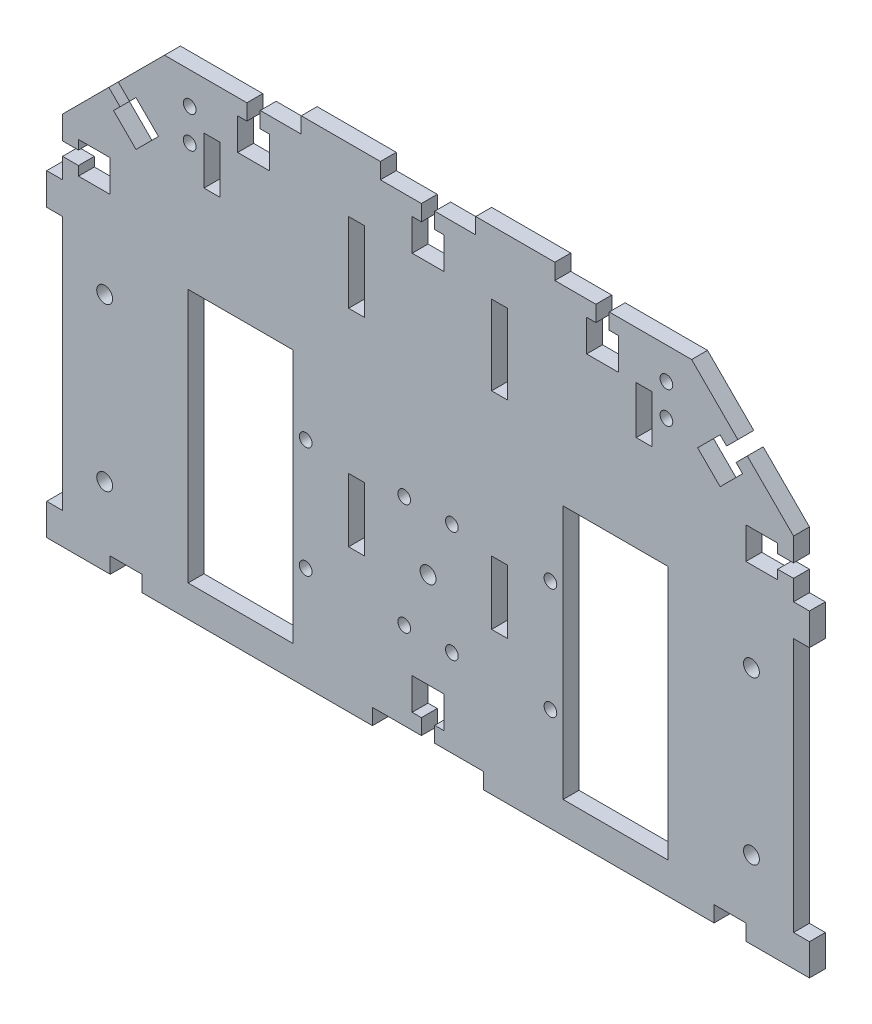
SolidWorks part; units mm, degrees
ref_plane "Front Plane" through (0, 0, 0) normal (0, 0, 1) x (1, 0, 0)
ref_plane "Top Plane" through (0, 0, 0) normal (0, 1, 0) x (1, 0, 0)
ref_plane "Right Plane" through (0, 0, 0) normal (1, 0, 0) x (0, 0, -1)
sketch "Sketch1" plane through (0, 0, 0) normal (0, 0, 1) x (1, 0, 0)
  line L28 (-42.5, -77.4) -> (-23.1006, -77.4) construction
  line L29 (42.5, -104.9) -> (-42.5, -104.9)
  line L30 (42.5, -104.9) -> (42.5, -49.9)
  line L32 (-42.5, -104.9) -> (-42.5, -49.9)
  line L57 (-42.5, -49.9) -> (-42.5, -37.4)
  line L58 (42.5, -49.9) -> (42.5, -37.4)
  line L89 (-120, -17.4) -> (-120, -37.4)
  line L91 (120, -37.4) -> (120, -17.4)
  line L101 (120, -17.4) -> (115, -17.4)
  line L102 (115, -17.4) -> (115, 12.8)
  line L103 (115, 12.8) -> (120, 12.8)
  line L104 (120, 12.8) -> (120, 27.7)
  line L105 (120, 27.7) -> (100.1, 27.7)
  line L106 (100.1, 27.7) -> (100.1, 22.7)
  line L107 (100.1, 22.7) -> (39.9, 22.7)
  line L108 (39.9, 22.7) -> (39.9, 27.7)
  line L109 (39.9, 27.7) -> (-39.9, 27.7)
  line L110 (-39.9, 27.7) -> (-39.9, 22.7)
  line L111 (-39.9, 22.7) -> (-100.1, 22.7)
  line L112 (-100.1, 22.7) -> (-100.1, 27.7)
  line L113 (-100.1, 27.7) -> (-120, 27.7)
  line L114 (-120, 27.7) -> (-120, 12.8)
  line L115 (-120, 12.8) -> (-115, 12.8)
  line L116 (-115, 12.8) -> (-115, -17.4)
  line L117 (-115, -17.4) -> (-120, -17.4)
  line L118 (-120, -37.4) -> (-42.5, -37.4)
  line L119 (42.5, -37.4) -> (120, -37.4)
  dimension "D1" = 20
  dimension "D2" = 85
  dimension "D3" = 55
  dimension "D4" = 20
  dimension "D5" = 12.5
  dimension "D6" = 65.1
extrude "Boss-Extrude1" add sketch "Sketch1" along normal blind 5
sketch "Sketch2" plane through (0, 0, 5) normal (0, 0, 1) x (1, 0, 0)
  line L0 (-42.5, -104.9) -> (-42.5, -117.4)
  line L1 (-42.5, -117.4) -> (-93, -117.4)
  line L2 (-120, -37.4) -> (-42.5, -37.4) construction
  line L3 (-93, -117.4) -> (-93, -37.4)
  line L4 (-93, -37.4) -> (-110.5, -37.4)
  line L5 (-110.5, -37.4) -> (-110.5, -117.4)
  line L6 (-2.1, -104.9) -> (2.1, -104.9)
  line L7 (-110.5, -117.4) -> (-120, -117.4)
  line L8 (-120, -117.4) -> (-120, -127.4)
  line L9 (-120, -127.4) -> (120, -127.4)
  line L13 (-2.1, -104.9) -> (-42.5, -104.9)
  line L15 (120, -117.4) -> (120, -127.4)
  line L16 (110.5, -117.4) -> (120, -117.4)
  line L17 (110.5, -37.4) -> (110.5, -117.4)
  line L18 (93, -37.4) -> (110.5, -37.4)
  line L19 (93, -117.4) -> (93, -37.4)
  line L20 (42.5, -117.4) -> (93, -117.4)
  line L21 (42.5, -104.9) -> (42.5, -117.4)
  line L22 (2.1, -104.9) -> (42.5, -104.9)
  dimension "D1" = 80
  dimension "D2" = 50.5
  dimension "D3" = 17.5
  dimension "D6" = 9.5
  dimension "D7" = 10
extrude "Boss-Extrude2" add sketch "Sketch2" against normal blind 5
sketch "Sketch3" plane through (0, 0, 5) normal (0, 0, 1) x (1, 0, 0)
  line L0 (-42.5, -77.4) -> (42.5, -77.4) construction
  line L1 (-42.5, -117.4) -> (-42.5, -37.4) construction
  line L2 (42.5, -117.4) -> (42.5, -37.4) construction
  line B0 (-42.5, -77.4) -> (-29.6234, -77.4) construction
  line B1 (-23, -59.9) -> (-23, -88.4652) construction
  line B2 (0, -54.9) -> (0, -85.8514) construction
  circle B3 centre (-38.5, -59.9) radius 2
  circle B4 centre (-38.5, -94.9) radius 2
  circle B5 centre (-7.5, -94.9) radius 2
  circle B6 centre (-7.5, -59.9) radius 2
  circle B7 centre (38.5, -94.9) radius 2
  circle B8 centre (7.5, -94.9) radius 2
  circle B9 centre (7.5, -59.9) radius 2
  circle B10 centre (38.5, -59.9) radius 2
  circle B11 centre (0, -77.4) radius 2.5
sketch_block_instance "Block1-1"
sketch_block "Block1" parameters "D1"=4, "D3"=5, "D2"=15.5
extrude "Cut-Extrude4" cut sketch "Sketch3" against normal blind 10
sketch "Sketch6" plane through (0, 0, 5) normal (0, 0, 1) x (1, 0, 0)
  line L0 (-93, -37.4) -> (-110.5, -37.4) construction
  line L1 (-110.5, -117.4) -> (-93, -117.4) construction
  line L2 (-101.75, -37.4) -> (-101.75, -117.4) construction
  line L3 (-101.75, -77.4) -> (-89.3082, -77.4) construction
  line L4 (0, -77.4) -> (0, -59.8253) construction
  line L5 (101.75, -77.4) -> (89.3082, -77.4) construction
  line L6 (101.75, -37.4) -> (101.75, -117.4) construction
  line L7 (110.5, -117.4) -> (93, -117.4) construction
  line L8 (93, -37.4) -> (110.5, -37.4) construction
  circle A0 centre (-101.75, -51.9) radius 2.5
  circle A1 centre (-101.75, -102.9) radius 2.5
  circle A2 centre (101.75, -102.9) radius 2.5
  circle A3 centre (101.75, -51.9) radius 2.5
  point P12 (-101.75, -77.4)
  dimension "D1" = 5
  dimension "D2" = 25.5
extrude "Cut-Extrude5" cut sketch "Sketch6" against normal blind 10
sketch "Sketch8" plane through (0, 0, 5) normal (0, 0, 1) x (1, 0, 0)
  line L3 (115, 22.7) -> (90, 22.7)
  line L4 (115, -2.3) -> (90, 22.7)
  line L5 (115, -2.3) -> (115, 22.7)
  line L6 (120, 12.8) -> (115, 12.8)
  line L7 (-100.1, 22.7) -> (-100.1, 27.7)
  line L8 (-100.1, 27.7) -> (-120, 27.7)
  line L9 (-120, 27.7) -> (-120, 12.8)
  line L10 (-120, 12.8) -> (-115, 12.8)
  line L12 (0, -7.3) -> (0, 6.6251) construction
  line L15 (-115, -2.3) -> (-115, 22.7)
  line L16 (-115, -2.3) -> (-90, 22.7)
  line L17 (-115, 22.7) -> (-90, 22.7)
  line L18 (-39.9, 22.7) -> (-100.1, 22.7) construction
  line L20 (-115, 12.8) -> (-115, -17.4) construction
  line L21 (120, 27.7) -> (120, 12.8)
  line L22 (100.1, 27.7) -> (120, 27.7)
  line L23 (100.1, 22.7) -> (100.1, 27.7)
  dimension "D1" = 25
  dimension "D2" = 25
extrude "Cut-Extrude6" cut sketch "Sketch8" against normal blind 10
sketch "Sketch9" plane through (0, 0, 5) normal (0, 0, 1) x (1, 0, 0)
  line L0 (-120, -127.4) -> (120, -127.4) construction
  line L1 (-17.5, -127.4) -> (17.5, -127.4)
  line L2 (-17.5, -127.4) -> (-17.5, -122.4)
  line L3 (-17.5, -122.4) -> (17.5, -122.4)
  line L4 (17.5, -127.4) -> (17.5, -122.4)
  line L6 (-2.1, -122.4) -> (2.1, -122.4)
  line L7 (-2.1, -122.4) -> (-2.1, -117.4)
  line L8 (-2.1, -117.4) -> (2.1, -117.4)
  line L9 (2.1, -122.4) -> (2.1, -117.4)
  line L10 (-5, -107.4) -> (5, -107.4)
  line L11 (-5, -107.4) -> (-5, -117.4)
  line L12 (-5, -117.4) -> (5, -117.4)
  line L13 (5, -107.4) -> (5, -117.4)
  line L17 (0, -127.4) -> (0, -136.2573) construction
  point P6 (0, -122.4)
  point P7 (0, -127.4)
  point P16 (0, -117.4)
  point P17 (0, -107.4)
  point P18 (0, -117.4)
  dimension "D1" = 5
  dimension "D2" = 35
  dimension "D3" = 10
  dimension "D4" = 10
  dimension "D5" = 5
  dimension "D6" = 4.2
  dimension "D7" = 5
extrude "Cut-Extrude7" cut sketch "Sketch9" against normal blind 10
sketch "Sketch10" plane through (-56.35, 56.35, 0) normal (-0.7071, 0.7071, 0) x (0, 0, 1)
  line L2 (-10.3693, -33.8009) -> (20.2296, -33.8009)
  line L3 (-10.3693, -33.8009) -> (-10.3693, -91.9489)
  line L4 (-10.3693, -91.9489) -> (20.2296, -91.9489)
  line L5 (20.2296, -33.8009) -> (20.2296, -91.9489)
extrude "Cut-Extrude8" cut sketch "Sketch10" against normal blind 5
mirror "Mirror1" about plane through (0, 0, 0) normal (1, 0, 0) of "Cut-Extrude8"
sketch "Sketch11" plane through (0, 0, 5) normal (0, 0, 1) x (1, 0, 0)
  line L0 (39.9, 27.7) -> (-39.9, 27.7) construction
  line L1 (15, 27.7) -> (-15, 27.7)
  line L2 (15, 27.7) -> (15, 22.7)
  line L3 (15, 22.7) -> (-15, 22.7)
  line L4 (-15, 27.7) -> (-15, 22.7)
  line L7 (-42.5, -117.4) -> (-93, -117.4) construction
  point P8 (0, 27.7)
  dimension "D1" = 30
  dimension "D2" = 15
  dimension "D3" = 140.1
extrude "Cut-Extrude9" cut sketch "Sketch11" against normal blind 5
sketch "Sketch12" plane through (110.5, 0, 0) normal (1, 0, 0) x (0, 0, -1)
  line L4 (-5, -37.4) -> (-5, -117.4)
  line L5 (-5, -117.4) -> (0, -117.4)
  line L6 (0, -117.4) -> (0, -37.4)
  line L7 (0, -37.4) -> (-5, -37.4)
  line L8 (-5, -37.4) -> (-5, -117.4)
  line L9 (-5, -117.4) -> (0, -117.4)
  line L10 (0, -117.4) -> (0, -37.4)
  line L13 (0, -37.4) -> (-5, -37.4)
  dimension "D1" = 0
extrude "Boss-Extrude3" add sketch "Sketch12" along normal blind 4.5
sketch "Sketch13" plane through (-110.5, 0, 0) normal (-1, 0, 0) x (0, 0, 1)
  line L4 (5, -117.4) -> (5, -37.4)
  line L5 (5, -37.4) -> (0, -37.4)
  line L6 (0, -37.4) -> (0, -117.4)
  line L7 (0, -117.4) -> (5, -117.4)
  line L8 (5, -117.4) -> (5, -37.4)
  line L9 (5, -37.4) -> (0, -37.4)
  line L10 (0, -37.4) -> (0, -117.4)
  line L11 (0, -117.4) -> (5, -117.4)
  dimension "D1" = 0
extrude "Boss-Extrude4" add sketch "Sketch13" along normal blind 4.5
sketch "Sketch14" plane through (0, -17.4, 0) normal (0, 1, 0) x (1, 0, 0)
  line L4 (120, 0) -> (115, 0)
  line L5 (115, 0) -> (115, -5)
  line L6 (115, -5) -> (120, -5)
  line L7 (120, -5) -> (120, 0)
  line L8 (120, 0) -> (115, 0)
  line L9 (115, 0) -> (115, -5)
  line L10 (115, -5) -> (120, -5)
  line L11 (120, -5) -> (120, 0)
  dimension "D1" = 0
extrude "Boss-Extrude5" add sketch "Sketch14" along normal blind 0.1
sketch "Sketch15" plane through (0, -37.4, 0) normal (0, -1, 0) x (1, 0, 0)
  line L4 (120, 5) -> (115, 5)
  line L5 (115, 5) -> (115, 0)
  line L6 (115, 0) -> (120, 0)
  line L7 (120, 0) -> (120, 5)
  line L8 (120, 5) -> (115, 5)
  line L9 (115, 5) -> (115, 0)
  line L10 (115, 0) -> (120, 0)
  line L11 (120, 0) -> (120, 5)
  dimension "D1" = 0
extrude "Cut-Extrude10" cut sketch "Sketch15" against normal blind 0.1
sketch "Sketch16" plane through (0, -17.4, 0) normal (0, 1, 0) x (1, 0, 0)
  line L4 (-115, 0) -> (-120, 0)
  line L5 (-120, 0) -> (-120, -5)
  line L6 (-120, -5) -> (-115, -5)
  line L7 (-115, -5) -> (-115, 0)
  line L8 (-115, 0) -> (-120, 0)
  line L9 (-120, 0) -> (-120, -5)
  line L10 (-120, -5) -> (-115, -5)
  line L11 (-115, -5) -> (-115, 0)
  dimension "D1" = 0
extrude "Boss-Extrude6" add sketch "Sketch16" along normal blind 0.1
sketch "Sketch17" plane through (0, -37.4, 0) normal (0, -1, 0) x (1, 0, 0)
  line L4 (-120, 0) -> (-115, 0)
  line L5 (-115, 0) -> (-115, 5)
  line L6 (-115, 5) -> (-120, 5)
  line L7 (-120, 5) -> (-120, 0)
  line L8 (-120, 0) -> (-115, 0)
  line L9 (-115, 0) -> (-115, 5)
  line L10 (-115, 5) -> (-120, 5)
  line L11 (-120, 5) -> (-120, 0)
  dimension "D1" = 0
extrude "Cut-Extrude11" cut sketch "Sketch17" against normal blind 0.1
sketch "Sketch18" plane through (0, -127.4, 0) normal (0, -1, 0) x (1, 0, 0)
  line L1 (167.3917, -79.5545) -> (-147.8839, -79.5545)
  line L2 (167.3917, -79.5545) -> (167.3917, 75.7177)
  line L3 (167.3917, 75.7177) -> (-147.8839, 75.7177)
  line L4 (-147.8839, -79.5545) -> (-147.8839, 75.7177)
extrude "Cut-Extrude12" cut sketch "Sketch18" against normal blind 0.1
sketch "Sketch19" plane through (0, -122.4, 0) normal (0, -1, 0) x (1, 0, 0)
  line L4 (2.1, 0) -> (17.5, 0) construction
  line L5 (17.5, 0) -> (17.5, 5) construction
  line L6 (17.5, 5) -> (2.1, 5) construction
  line L7 (2.1, 5) -> (2.1, 0) construction
  line L12 (-17.5, 0) -> (-2.1, 0) construction
  line L13 (-2.1, 0) -> (-2.1, 5) construction
  line L14 (-2.1, 5) -> (-17.5, 5) construction
  line L15 (-17.5, 5) -> (-17.5, 0) construction
  line L20 (2.1, 0) -> (17.5, 0)
  line L21 (17.5, 0) -> (17.5, 5)
  line L22 (17.5, 5) -> (2.1, 5)
  line L23 (2.1, 5) -> (2.1, 0)
  line L28 (-17.5, 0) -> (-2.1, 0)
  line L29 (-2.1, 0) -> (-2.1, 5)
  line L30 (-2.1, 5) -> (-17.5, 5)
  line L31 (-17.5, 5) -> (-17.5, 0)
extrude "Cut-Extrude13" cut sketch "Sketch19" against normal blind 0.1
sketch "Sketch20" plane through (0, 0, 5) normal (0, 0, 1) x (1, 0, 0)
  line L0 (-97.4795, 8.1494) -> (-100.4494, 5.1795)
  line L1 (-97.4795, 8.1494) -> (-93.944, 4.6139)
  line L2 (-100.4494, 5.1795) -> (-96.9139, 1.644)
  line L3 (-93.944, 4.6139) -> (-96.9139, 1.644)
  line L4 (-82.9289, 22.7) -> (-115, -9.3711) construction
  line L5 (-91.8934, 6.6645) -> (-98.9645, -0.4066)
  line L6 (-91.8934, 6.6645) -> (-84.8223, -0.4066)
  line L7 (-98.9645, -0.4066) -> (-91.8934, -7.4777)
  line L8 (-84.8223, -0.4066) -> (-91.8934, -7.4777)
  line L9 (-95.4289, 3.1289) -> (-93.1759, 0.8759) construction
  point P6 (-95.4289, 3.1289)
  point P9 (-95.4289, 3.1289)
  point P14 (-88.3579, -3.9421)
  point P16 (-98.9645, 6.6645)
  point P17 (-98.9645, 6.6645)
  dimension "D1" = 10
  dimension "D2" = 4.2
  dimension "D3" = 5
  dimension "D4" = 10
extrude "Cut-Extrude14" cut sketch "Sketch20" against normal blind 5
mirror "Mirror2" about plane through (0, 0, 0) normal (1, 0, 0) of "Cut-Extrude14"
sketch "Sketch21" plane through (0, 0, 5) normal (0, 0, 1) x (1, 0, 0)
  line L0 (-115, -9.3711) -> (-115, -17.3) construction
  line L1 (-115, -20.9) -> (-105, -20.9)
  line L2 (-115, -20.9) -> (-115, -16.7)
  line L3 (-115, -16.7) -> (-105, -16.7)
  line L4 (-105, -20.9) -> (-105, -16.7)
  line L10 (-115, -37.3) -> (-120, -37.3) construction
  line L11 (-110, -15.3) -> (-106.8, -15.3)
  line L12 (-110, -15.3) -> (-110, -22.3)
  line L13 (-110, -22.3) -> (-106.8, -22.3)
  line L14 (-106.8, -15.3) -> (-106.8, -22.3)
  point P10 (-115, -18.8)
  point P11 (-110, -18.8)
  point P12 (-105, -18.8)
  dimension "D1" = 7
  dimension "D2" = 3.2
  dimension "D3" = 10
  dimension "D4" = 4.2
  dimension "D5" = 18.5
  dimension "D6" = 5
extrude "Cut-Extrude15" cut sketch "Sketch21" against normal blind 5 contours L12 L3 L2 L1 | L14 L3 L12 L1 | L3 L14 L1 L4 | L14 L11 L12 L3 | L14 L1 L12 L13
sketch "Sketch22" plane through (0, 0, 5) normal (0, 0, 1) x (1, 0, 0)
  line L1 (25, -82.3) -> (20, -82.3)
  line L2 (25, -82.3) -> (25, -57.3)
  line L3 (25, -57.3) -> (20, -57.3)
  line L4 (20, -82.3) -> (20, -57.3)
  line L5 (82.9289, 22.7) -> (39.9, 22.7) construction
  line L6 (115, -37.3) -> (115, -117.4) construction
  line L7 (32.3404, -37.3) -> (14.5847, -37.3) construction
  line L8 (25, -17.3) -> (20, -17.3)
  line L9 (25, 7.7) -> (25, -17.3)
  line L10 (25, 7.7) -> (20, 7.7)
  line L11 (20, 7.7) -> (20, -17.3)
  line L12 (0, 22.7) -> (0, 14.282) construction
  line L13 (-15, 22.7) -> (15, 22.7) construction
  line L14 (-32.3404, -37.3) -> (-14.5847, -37.3) construction
  line L15 (-20, 7.7) -> (-20, -17.3)
  line L16 (-25, 7.7) -> (-20, 7.7)
  line L17 (-25, 7.7) -> (-25, -17.3)
  line L18 (-25, -17.3) -> (-20, -17.3)
  line L19 (-20, -82.3) -> (-20, -57.3)
  line L20 (-25, -57.3) -> (-20, -57.3)
  line L21 (-25, -82.3) -> (-25, -57.3)
  line L22 (-25, -82.3) -> (-20, -82.3)
  dimension "D5" = 20
  dimension "D1" = 25
  dimension "D2" = 80
  dimension "D3" = 90
  dimension "D4" = 5
extrude "Cut-Extrude16" cut sketch "Sketch22" against normal blind 10
sketch "Sketch23" plane through (0, 0, 5) normal (0, 0, 1) x (1, 0, 0)
  line L0 (82.9289, 22.7) -> (39.9, 22.7) construction
  line L1 (115, -17.3) -> (115, -9.3711) construction
  line L5 (0, 0) -> (0, 16.8102) construction
  circle A0 centre (75, 12.7) radius 2
  circle A1 centre (75, 2.7) radius 2
  circle A4 centre (-75, 2.7) radius 2
  circle A5 centre (-75, 12.7) radius 2
  dimension "D1" = 4
  dimension "D2" = 10
  dimension "D3" = 40
  dimension "D4" = 4
  dimension "D5" = 20
  dimension "D6" = 40
extrude "Cut-Extrude17" cut sketch "Sketch23" against normal blind 10
mirror "Mirror3" about plane through (0, 0, 0) normal (1, 0, 0) of "Cut-Extrude15"
sketch "Sketch24" plane through (0, 0, 5) normal (0, 0, 1) x (1, 0, 0)
  line L0 (-39.9, 22.7) -> (-82.9289, 22.7) construction
  line L1 (-52.8, 22.7) -> (-57, 22.7)
  line L2 (-52.8, 22.7) -> (-52.8, 17.7)
  line L3 (-52.8, 17.7) -> (-57, 17.7)
  line L4 (-57, 22.7) -> (-57, 17.7)
  line L5 (-39.9, 27.7) -> (-39.9, 22.7) construction
  line L6 (-49.9, 17.7) -> (-59.9, 17.7)
  line L7 (-49.9, 17.7) -> (-49.9, 7.7)
  line L8 (-49.9, 7.7) -> (-59.9, 7.7)
  line L9 (-59.9, 17.7) -> (-59.9, 7.7)
  line L10 (0, 22.7) -> (0, 9.5) construction
  line L11 (-15, 22.7) -> (15, 22.7) construction
  line L12 (59.9, 17.7) -> (59.9, 7.7)
  line L13 (49.9, 7.7) -> (59.9, 7.7)
  line L14 (49.9, 17.7) -> (49.9, 7.7)
  line L15 (49.9, 17.7) -> (59.9, 17.7)
  line L16 (57, 22.7) -> (57, 17.7)
  line L17 (52.8, 17.7) -> (57, 17.7)
  line L18 (52.8, 22.7) -> (52.8, 17.7)
  line L19 (52.8, 22.7) -> (57, 22.7)
  line L21 (2.1, 22.7) -> (-2.1, 22.7)
  line L22 (2.1, 22.7) -> (2.1, 17.7)
  line L23 (2.1, 17.7) -> (-2.1, 17.7)
  line L24 (-2.1, 22.7) -> (-2.1, 17.7)
  line L25 (-5, 17.7) -> (5, 17.7)
  line L26 (-5, 17.7) -> (-5, 7.7)
  line L27 (-5, 7.7) -> (5, 7.7)
  line L28 (5, 17.7) -> (5, 7.7)
  point P10 (-54.9, 17.7)
  point P11 (-54.9, 17.7)
  point P14 (-54.9, 22.7)
  point P36 (0, 17.7)
  point P37 (0, 17.7)
  point P39 (0, 22.7)
  dimension "D1" = 5
  dimension "D2" = 10
  dimension "D3" = 15
  dimension "D4" = 4.2
  dimension "D5" = 10
  dimension "D6" = 5
  dimension "D7" = 10
  dimension "D8" = 4.2
  dimension "D9" = 10
extrude "Cut-Extrude18" cut sketch "Sketch24" against normal blind 10 contours L15 L14 L13 L12 | L19 L18 L15 L16 | L10 L25 L26 L27 | L23 L10 L27 L28 L25 | L6 L9 L8 L7 L3 | L1 L4 L3 L2
sketch "Sketch25" plane through (0, 0, 5) normal (0, 0, 1) x (1, 0, 0)
  line L0 (-20, -82.3) -> (-20, -57.3) construction
  line L1 (-25, -57.3) -> (-20, -57.3)
  line L2 (-25, -57.3) -> (-25, -62.3)
  line L3 (-25, -62.3) -> (-20, -62.3)
  line L4 (-20, -57.3) -> (-20, -62.3)
  line L5 (25, -82.3) -> (25, -57.3) construction
  line L6 (20, -57.3) -> (25, -57.3)
  line L7 (20, -57.3) -> (20, -62.3)
  line L8 (20, -62.3) -> (25, -62.3)
  line L9 (25, -57.3) -> (25, -62.3)
  dimension "D1" = 5
  dimension "D2" = 5
extrude "Boss-Extrude7" add sketch "Sketch25" against normal blind 5
sketch "Sketch26" plane through (93, 0, 0) normal (-1, 0, 0) x (0, 0, 1)
  line L4 (5, -117.4) -> (5, -37.4)
  line L5 (5, -37.4) -> (0, -37.4)
  line L6 (0, -37.4) -> (0, -117.4)
  line L7 (0, -117.4) -> (5, -117.4)
  line L8 (5, -117.4) -> (5, -37.4)
  line L9 (5, -37.4) -> (0, -37.4)
  line L10 (0, -37.4) -> (0, -117.4)
  line L11 (0, -117.4) -> (5, -117.4)
  dimension "D1" = 0
extrude "Boss-Extrude8" [suppressed] add sketch "Sketch26" along normal blind 10
sketch "Sketch27" plane through (-93, 0, 0) normal (1, 0, 0) x (0, 0, -1)
  line L4 (-5, -37.4) -> (-5, -117.4)
  line L5 (-5, -117.4) -> (0, -117.4)
  line L6 (0, -117.4) -> (0, -37.4)
  line L7 (0, -37.4) -> (-5, -37.4)
  line L8 (-5, -37.4) -> (-5, -117.4)
  line L9 (-5, -117.4) -> (0, -117.4)
  line L10 (0, -117.4) -> (0, -37.4)
  line L11 (0, -37.4) -> (-5, -37.4)
  dimension "D1" = 0
extrude "Boss-Extrude9" [suppressed] add sketch "Sketch27" along normal blind 10
sketch "Sketch28" plane through (0, 0, 5) normal (0, 0, 1) x (1, 0, 0)
  line L0 (-120, -127.3) -> (-17.5, -127.3) construction
  line L1 (-90, -127.3) -> (-100, -127.3)
  line L2 (-90, -127.3) -> (-90, -122.3)
  line L3 (-90, -122.3) -> (-100, -122.3)
  line L4 (-100, -127.3) -> (-100, -122.3)
  line L5 (-115, -117.4) -> (-115, -37.3) construction
  line L6 (0, -107.4) -> (0, -98.8418) construction
  line L7 (-5, -107.4) -> (5, -107.4) construction
  line L8 (100, -127.3) -> (100, -122.3)
  line L9 (90, -122.3) -> (100, -122.3)
  line L10 (90, -127.3) -> (90, -122.3)
  line L11 (90, -127.3) -> (100, -127.3)
  dimension "D1" = 5
  dimension "D2" = 10
  dimension "D3" = 15
extrude "Cut-Extrude19" cut sketch "Sketch28" against normal blind 5
sketch "Sketch30" plane through (0, 0, 5) normal (0, 0, 1) x (1, 0, 0)
  line L0 (-57, 22.7) -> (-82.9289, 22.7) construction
  line L1 (-65.5, -7.3) -> (-70.5, -7.3)
  line L2 (-65.5, -7.3) -> (-65.5, 7.7)
  line L3 (-65.5, 7.7) -> (-70.5, 7.7)
  line L4 (-70.5, -7.3) -> (-70.5, 7.7)
  line L5 (-93, -117.4) -> (-93, -37.4) construction
  line L6 (0, 7.7) -> (0, 5.4914) construction
  line L7 (-5, 7.7) -> (5, 7.7) construction
  line L8 (70.5, -7.3) -> (70.5, 7.7)
  line L9 (65.5, 7.7) -> (70.5, 7.7)
  line L10 (65.5, -7.3) -> (65.5, 7.7)
  line L11 (65.5, -7.3) -> (70.5, -7.3)
  point P4 (-68, 7.7)
  dimension "D1" = 15
  dimension "D2" = 5
  dimension "D3" = 15
  dimension "D4" = 27.5
extrude "Cut-Extrude21" cut sketch "Sketch30" against normal blind 5
sketch "Sketch31" plane through (0, 0, 5) normal (0, 0, 1) x (1, 0, 0)
  line L1 (105, -20.9) -> (105, -16.7) construction
  line L2 (110, -13.8) -> (100, -13.8)
  line L3 (110, -13.8) -> (110, -23.8)
  line L4 (110, -23.8) -> (100, -23.8)
  line L5 (100, -13.8) -> (100, -23.8)
  line L6 (110, -20.9) -> (110, -22.3) construction
  line L7 (0, 0) -> (0, -18.8832) construction
  line L8 (-100, -13.8) -> (-100, -23.8)
  line L9 (-110, -23.8) -> (-100, -23.8)
  line L10 (-110, -13.8) -> (-110, -23.8)
  line L11 (-110, -13.8) -> (-100, -13.8)
  point P0 (110, -18.8)
  point P7 (105, -18.8)
  dimension "D1" = 10
  dimension "D2" = 10
extrude "Cut-Extrude22" cut sketch "Sketch31" against normal blind 10
sketch "Sketch32" plane through (0, 0, 5) normal (0, 0, 1) x (1, 0, 0)
  line L0 (-120, -17.3) -> (-115, -17.3) construction
  line L1 (-120, -17.3) -> (-120, -37.3) construction
  line L2 (-120, -17.3) -> (-115, -17.3)
  line L3 (-120, -17.3) -> (-120, -37.3)
  line L4 (-115, -17.3) -> (-115, -27.3)
  line L5 (-115, -27.3) -> (-120, -27.3)
  dimension "D1" = 10
extrude "Cut-Extrude23" cut sketch "Sketch32" against normal blind 5 contours L5 L4 L2 L3
sketch "Sketch33" plane through (0, 0, 5) normal (0, 0, 1) x (1, 0, 0)
  line L1 (120, -17.3) -> (115, -17.3)
  line L2 (120, -17.3) -> (120, -27.3)
  line L3 (120, -27.3) -> (115, -27.3)
  line L4 (115, -17.3) -> (115, -27.3)
  dimension "D1" = 5
  dimension "D2" = 10
extrude "Cut-Extrude24" cut sketch "Sketch33" against normal blind 5
sketch "Sketch34" plane through (93, 0, 0) normal (-1, 0, 0) x (0, 0, 1)
  line L4 (5, -117.4) -> (5, -37.4)
  line L5 (5, -37.4) -> (0, -37.4)
  line L6 (0, -37.4) -> (0, -117.4)
  line L7 (0, -117.4) -> (5, -117.4)
  line L8 (5, -117.4) -> (5, -37.4)
  line L9 (5, -37.4) -> (0, -37.4)
  line L10 (0, -37.4) -> (0, -117.4)
  line L11 (0, -117.4) -> (5, -117.4)
  dimension "D1" = 0
extrude "Boss-Extrude10" add sketch "Sketch34" along normal blind 17.5
sketch "Sketch35" plane through (-93, 0, 0) normal (1, 0, 0) x (0, 0, -1)
  line L4 (-5, -37.4) -> (-5, -117.4)
  line L5 (-5, -117.4) -> (0, -117.4)
  line L6 (0, -117.4) -> (0, -37.4)
  line L7 (0, -37.4) -> (-5, -37.4)
  line L8 (-5, -37.4) -> (-5, -117.4)
  line L9 (-5, -117.4) -> (0, -117.4)
  line L10 (0, -117.4) -> (0, -37.4)
  line L11 (0, -37.4) -> (-5, -37.4)
  dimension "D1" = 0
extrude "Boss-Extrude11" add sketch "Sketch35" along normal blind 17.5
